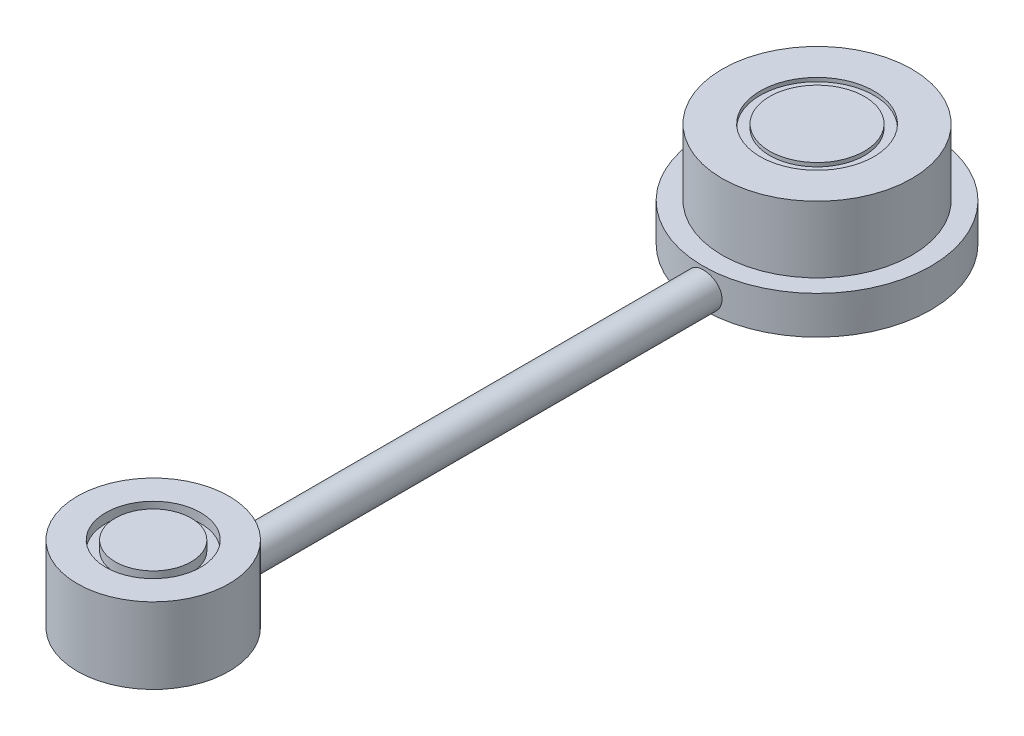
SolidWorks part; units mm, degrees
ref_plane "Front Plane" through (0, 0, 0) normal (0, 0, 1) x (1, 0, 0)
ref_plane "Top Plane" through (0, 0, 0) normal (0, 1, 0) x (1, 0, 0)
ref_plane "Right Plane" through (0, 0, 0) normal (1, 0, 0) x (0, 0, -1)
sketch "Sketch2" plane through (0, 0, 0) normal (0, 1, 0) x (1, 0, 0)
  circle A0 centre (0, 0) radius 15.24
  dimension "D1" = 30.48
extrude "Boss-Extrude1" add sketch "Sketch2" along normal blind 5.08
sketch "Sketch3" plane through (0, 5.08, 0) normal (0, 1, 0) x (1, 0, 0)
  circle A0 centre (0, 0) radius 12.7
  dimension "D1" = 25.4
extrude "Boss-Extrude4" add sketch "Sketch3" along normal blind 8.89
sketch "Sketch4" plane through (0, 13.97, 0) normal (0, 1, 0) x (1, 0, 0)
  circle A0 centre (0, 0) radius 7.62
  circle A1 centre (0, 0) radius 6.35
  dimension "D1" = 12.7
extrude "Cut-Extrude2" cut sketch "Sketch4" against normal blind 0.508
sketch "Sketch6" plane through (0, 0, 0) normal (0, -1, 0) x (1, 0, 0)
  line L0 (0, 0) -> (0, 88.9) construction
  circle A0 centre (0, 88.9) radius 10.16
  dimension "D1" = 88.9
sketch "Sketch7" plane through (0, 0, 0) normal (0, 1, 0) x (1, 0, 0)
  circle A0 centre (0, -88.9) radius 10.16
extrude "Boss-Extrude7" add sketch "Sketch7" along normal blind 10.16 separate body
sketch "Sketch8" plane through (0, 10.16, 0) normal (0, 1, 0) x (1, 0, 0)
  circle A0 centre (0, -88.9) radius 6.35
  circle A1 centre (0, -88.9) radius 5.08
extrude "Cut-Extrude6" cut sketch "Sketch8" against normal blind 1.27
sketch "Sketch10" plane through (0, 0, 0) normal (0, 0, 1) x (1, 0, 0)
  line L0 (0, 0) -> (-7.62, 0)
  line L1 (-10.16, 0) -> (10.16, 0) construction
  line L2 (0, 0) -> (7.8065, 0)
  arc A0 (7.8065, 0) -> (-7.62, 0) centre (0.0933, 0) ccw
sketch "Sketch11" plane through (0, 0, 0) normal (0, 0, 1) x (1, 0, 0)
  circle A0 centre (0, 2.3246) radius 2.3354
extrude "Boss-Extrude8" add sketch "Sketch11" along normal blind 82.55
sketch "Sketch12" plane through (0, 0, 0) normal (0, -1, 0) x (1, 0, 0)
  circle A0 centre (-0.225, 0) radius 6.35
  dimension "D1" = 12.7
extrude "Boss-Extrude9" add sketch "Sketch12" along normal blind 2.54
sketch "Sketch13" plane through (0, 0, 0) normal (0, -1, 0) x (1, 0, 0)
  circle A0 centre (0, 88.9) radius 5.715
  dimension "D1" = 11.43
extrude "Boss-Extrude13" add sketch "Sketch13" along normal blind 1.905
